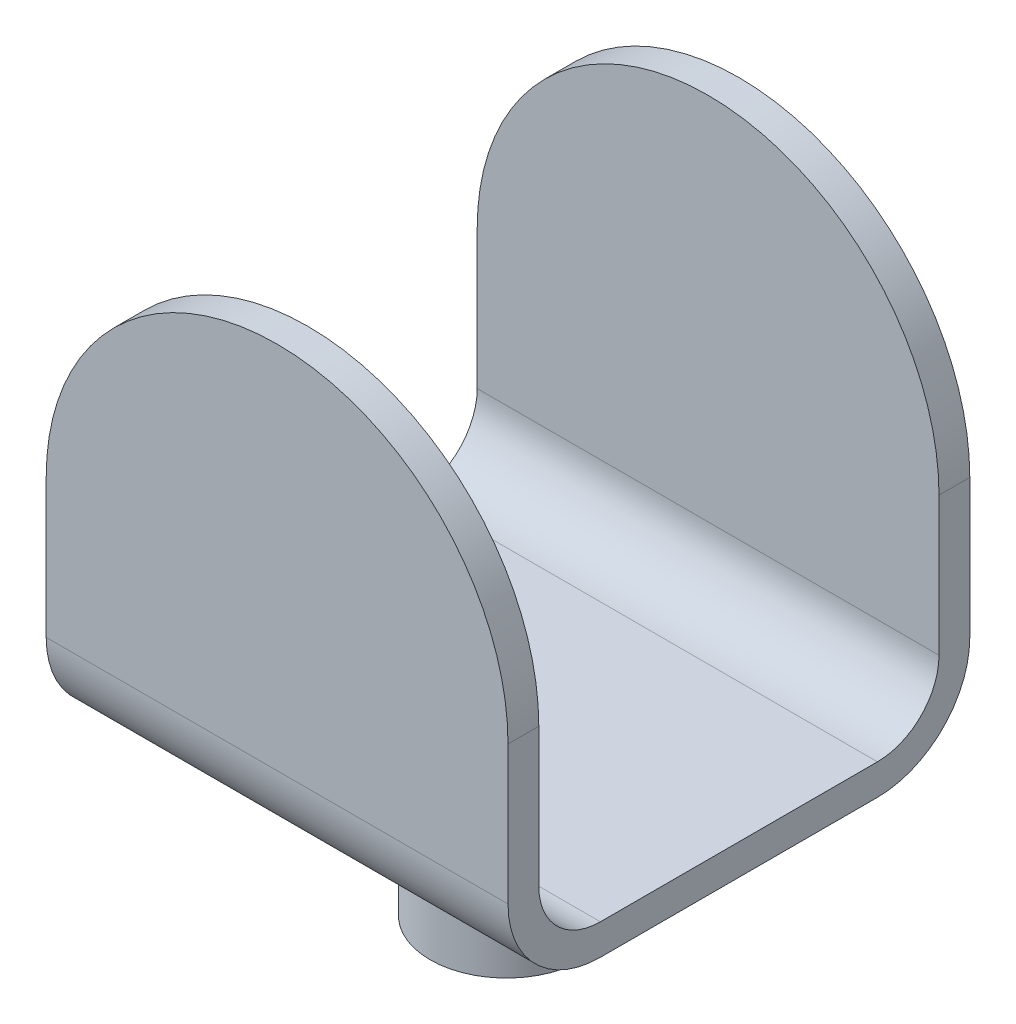
SolidWorks part; units mm, degrees
ref_plane "Front Plane" through (0, 0, 0) normal (0, 0, 1) x (1, 0, 0)
ref_plane "Top Plane" through (0, 0, 0) normal (0, 1, 0) x (1, 0, 0)
ref_plane "Right Plane" through (0, 0, 0) normal (1, 0, 0) x (0, 0, -1)
sketch "Sketch1" plane through (0, 0, 0) normal (0, 0, 1) x (1, 0, 0)
  line L1 (0, 0) -> (76.207, 0)
  line L2 (0, 0) -> (0, 76.207)
  line L3 (0, 76.207) -> (76.207, 76.207)
  line L4 (76.207, 0) -> (76.207, 76.207)
extrude "Boss-Extrude1" add sketch "Sketch1" along normal blind 76.2 contours L3 L4 L1 L2
ref_plane "Plane1" through (76.207, 76.207, 0) normal (1, 0, 0) x (0, 0, -1)
fillet "Fillet1" radius 15.24 2 edges at (38.1035, 0, 76.2) (38.1035, 0, 0)
fillet "Fillet4" radius 38.1035 4 edges at (38.1035, 76.207, 0) (76.207, 76.207, 38.1) (0, 76.207, 38.1) (38.1035, 76.207, 76.2)
sketch "Sketch3" plane through (76.207, 0, 0) normal (1, 0, 0) x (0, 0, -1)
  line L46 (-71.12, 76.207) -> (-5.08, 76.207)
  line L51 (-60.96, 5.08) -> (-15.24, 5.08)
  line L52 (-5.08, 15.24) -> (-5.08, 38.1035)
  line L53 (-5.08, 38.1035) -> (-5.08, 76.207)
  line L54 (-71.12, 38.1035) -> (-71.12, 15.24)
  line L55 (-71.12, 76.207) -> (-71.12, 38.1035)
  line L56 (-60.96, 5.08) -> (-15.24, 5.08)
  line L57 (-5.08, 15.24) -> (-5.08, 38.1035)
  line L58 (-5.08, 38.1035) -> (-5.08, 76.207)
  line L59 (-71.12, 38.1035) -> (-71.12, 15.24)
  line L60 (-71.12, 76.207) -> (-71.12, 38.1035)
  arc A17 (-71.12, 15.24) -> (-60.96, 5.08) centre (-60.96, 15.24) ccw
  arc A18 (-15.24, 5.08) -> (-5.08, 15.24) centre (-15.24, 15.24) ccw
  arc A19 (-71.12, 15.24) -> (-60.96, 5.08) centre (-60.96, 15.24) ccw
  arc A20 (-15.24, 5.08) -> (-5.08, 15.24) centre (-15.24, 15.24) ccw
  dimension "D1" = 5.08
extrude "Cut-Extrude1" cut sketch "Sketch3" against normal blind 207.518
sketch "Sketch4" plane through (0, 0, 0) normal (0, -1, 0) x (-1, 0, 0)
  circle A0 centre (-37.114, -37.3517) radius 12.6155
extrude "Boss-Extrude2" add sketch "Sketch4" along normal blind 25.4
